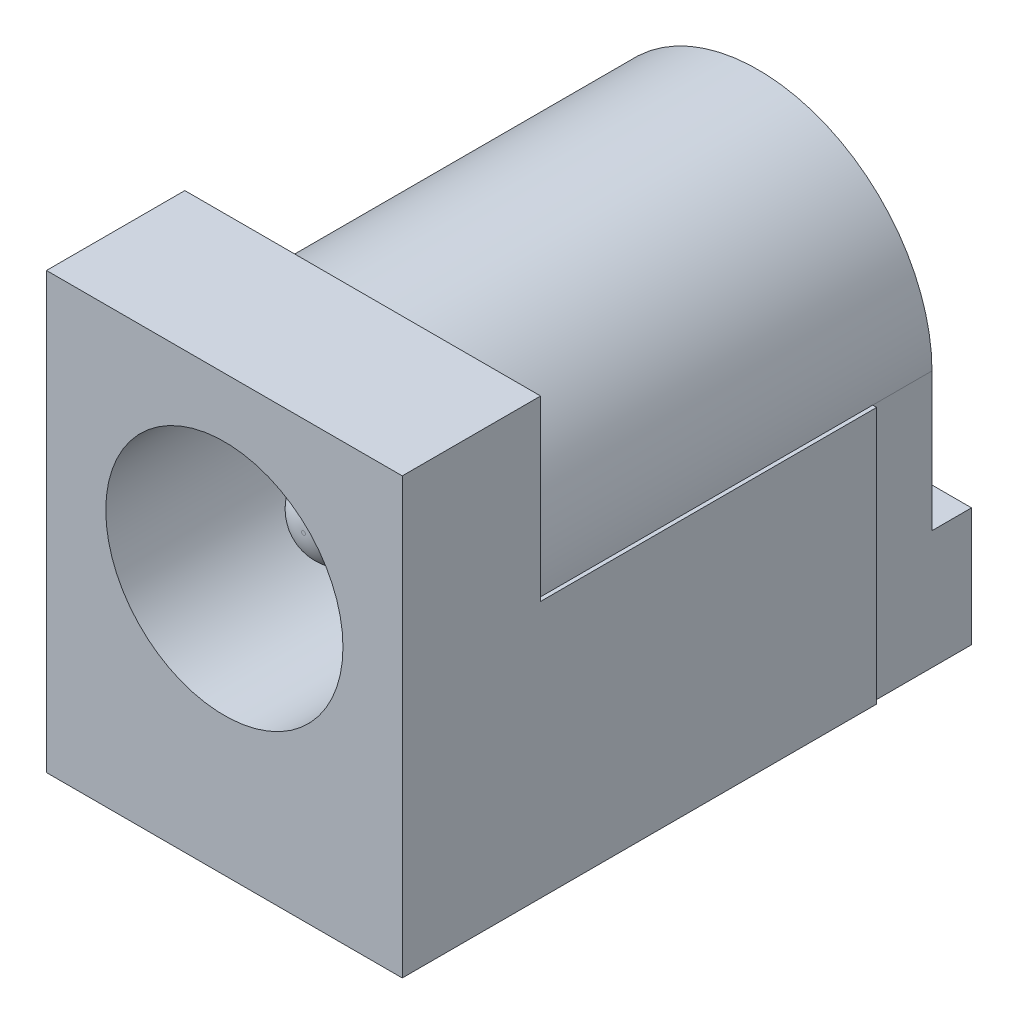
SolidWorks part; units mm, degrees
ref_plane "Front Plane" through (0, 0, 0) normal (0, 0, 1) x (1, 0, 0)
ref_plane "Top Plane" through (0, 0, 0) normal (0, 1, 0) x (1, 0, 0)
ref_plane "Right Plane" through (0, 0, 0) normal (1, 0, 0) x (0, 0, -1)
sketch "Sketch1" plane through (0, 0, 0) normal (1, 0, 0) x (0, 0, -1)
  line L1 (0, 0) -> (14.5, 0)
  line L2 (0, 0) -> (0, 11)
  line L3 (0, 11) -> (14.5, 11)
  line L4 (14.5, 0) -> (14.5, 11)
  dimension "D1" = 11
  dimension "D2" = 14.5
extrude "Boss-Extrude1" add sketch "Sketch1" along normal blind 9
sketch "Sketch2" plane through (0, 0, -14.5) normal (0, 0, -1) x (-1, 0, 0)
  line L0 (-8.9, 6.5) -> (-9, 6.5)
  line L4 (-9, 0) -> (-9, 11) construction
  line L5 (-0.1, 6.5) -> (0, 6.5)
  line L6 (0, 0) -> (0, 11) construction
  line L7 (-9, 11) -> (0, 11) construction
  arc A0 (-8.9, 6.5) -> (-0.1, 6.5) centre (-4.5, 6.5) cw
  dimension "D2" = 4.4
  dimension "D1" = 4.5
  dimension "D3" = 0.1
extrude "Cut-Extrude1" cut sketch "Sketch2" against normal blind 11 and the other way through all
sketch "Sketch5" plane through (0, 0, 0) normal (-1, 0, 0) x (0, 0, 1)
  line L0 (-14.5, 6.5) -> (-3.5, 6.5) construction
  line L1 (-14.5, 0) -> (-12, 0)
  line L2 (-14.5, 0) -> (-14.5, 6.5)
  line L3 (-14.5, 6.5) -> (-12, 6.5)
  line L4 (-12, 0) -> (-12, 6.5)
  dimension "D1" = 2.5
extrude "Cut-Extrude2" cut sketch "Sketch5" against normal blind 0.1
sketch "Sketch6" plane through (9, 0, 0) normal (1, 0, 0) x (0, 0, -1)
  line L0 (14.5, 6.5) -> (3.5, 6.5) construction
  line L1 (14.5, 0) -> (12, 0)
  line L2 (14.5, 0) -> (14.5, 6.5)
  line L3 (14.5, 6.5) -> (12, 6.5)
  line L4 (12, 0) -> (12, 6.5)
  dimension "D1" = 2.5
extrude "Cut-Extrude3" cut sketch "Sketch6" against normal blind 0.1
sketch "Sketch7" plane through (0, 0, -14.5) normal (0, 0, -1) x (-1, 0, 0)
  line L2 (-8.9, 6.5) -> (-8.9, 0)
  line L3 (-8.9, 0) -> (-0.1, 0)
  line L4 (-0.1, 6.5) -> (-0.1, 0)
  arc A0 (-8.9, 6.5) -> (-0.1, 6.5) centre (-4.5, 6.5) cw
  arc A1 (-0.1, 6.5) -> (-8.9, 6.5) centre (-4.5, 6.5) ccw construction
  dimension "D1" = 4.4
extrude "Cut-Extrude4" cut sketch "Sketch7" against normal blind 1
sketch "Sketch8" plane through (0, 0, -13.5) normal (0, 0, -1) x (-1, 0, 0)
  line L1 (-8.9, 0) -> (-6, 0)
  line L2 (-8.9, 0) -> (-8.9, 3)
  line L3 (-8.9, 3) -> (-6, 3)
  line L4 (-6, 0) -> (-6, 3)
  line L5 (-0.1, 0) -> (-3, 0)
  line L6 (-0.1, 0) -> (-0.1, 3)
  line L7 (-0.1, 3) -> (-3, 3)
  line L8 (-3, 0) -> (-3, 3)
  dimension "D1" = 3
  dimension "D2" = 2.9
  dimension "D3" = 2.9
  dimension "D4" = 3
extrude "Boss-Extrude2" add sketch "Sketch8" along normal blind 1
sketch "Sketch9" plane through (0, 0, 0) normal (0, 0, 1) x (1, 0, 0)
  line L0 (9, 11) -> (0, 11) construction
  line L1 (0, 11) -> (0, 0) construction
  circle A0 centre (4.5, 6.5) radius 3
  dimension "D3" = 6
  dimension "D1" = 4.5
  dimension "D2" = 4.5
extrude "Cut-Extrude5" cut sketch "Sketch9" against normal blind 12
sketch "Sketch10" plane through (0, 0, -13.5) normal (0, 0, -1) x (-1, 0, 0)
  line L2 (-9, 11) -> (0, 11) construction
  line L4 (-6, 0) -> (-6, 5.3176)
  line L6 (-2.9977, 0) -> (-2.9977, 5.3204)
  line L8 (-9, 6.5) -> (-9, 0) construction
  line L11 (-6, 0) -> (-6, -3.5)
  line L12 (-6, -3.5) -> (-2.9977, -3.5)
  line L13 (-2.9977, 0) -> (-2.9977, -3.5)
  arc A1 (-6, 5.3176) -> (-2.9977, 5.3204) centre (-4.5, 6.5) cw
  dimension "D4" = 5.3204
  dimension "D3" = 1.91
  dimension "D1" = 4.5
  dimension "D2" = 4.5
  dimension "D5" = 3.5
  dimension "D6" = 3.5
extrude "Boss-Extrude4" add sketch "Sketch10" along normal blind 0.4 separate body
sketch "Sketch11" plane through (0, 0, -13.9) normal (0, 0, -1) x (-1, 0, 0)
  line L0 (-3, 0) -> (-0.1, 0) construction
  line L2 (-9, 6.5) -> (-9, 0) construction
  circle A0 centre (-4.5, 1.5) radius 0.5
  dimension "D3" = 1
  dimension "D1" = 1.5
  dimension "D2" = 4.5
extrude "Boss-Extrude5" add sketch "Sketch11" along normal blind 0.1 draft 80
fillet "Fillet1" radius 1.4 2 edges at (6, -3.5, -13.7) (2.9977, -3.5, -13.7)
sketch "Sketch12" plane through (0, 0, -13.9) normal (0, 0, -1) x (-1, 0, 0)
  line L0 (-4.6, -3.5) -> (-4.3977, -3.5) construction
  circle A0 centre (-4.4747, -2) radius 0.8
  dimension "D2" = 1.6
  dimension "D1" = 1.5
extrude "Cut-Extrude6" cut sketch "Sketch12" against normal blind 0.4
sketch "Sketch13" plane through (0, 0, -13.9) normal (0, 0, -1) x (-1, 0, 0)
  line L0 (-9, 6.5) -> (-9, 11) construction
  line L1 (-9, 11) -> (0, 11) construction
  circle A0 centre (-4.5042, 6.5) radius 1.5
  circle A1 centre (-4.5042, 6.5) radius 1
  dimension "D3" = 3
  dimension "D4" = 2
  dimension "D1" = 4.4958
  dimension "D2" = 4.5
extrude "Boss-Extrude6" add sketch "Sketch13" along normal blind 0.2 draft 35 separate body
sketch "Sketch14" plane through (0, 0, -13.9) normal (0, 0, -1) x (-1, 0, 0)
  circle A0 centre (-4.5042, 6.5) radius 0.8
  dimension "D1" = 1.6
extrude "Cut-Extrude7" cut sketch "Sketch14" against normal blind 0.1 draft 85
sketch "Sketch16" plane through (0, 0, 0) normal (0, -1, 0) x (1, 0, 0)
  line L0 (9, 0) -> (0, 0) construction
  line L1 (3.25, -7.7) -> (5.75, -7.7)
  line L2 (3.25, -7.7) -> (3.25, -8.1)
  line L3 (3.25, -8.1) -> (5.75, -8.1)
  line L4 (5.75, -7.7) -> (5.75, -8.1)
  line L5 (0, 0) -> (0, -12) construction
  dimension "D1" = 7.7
  dimension "D2" = 2.5
  dimension "D3" = 3.25
  dimension "D4" = 0.4
extrude "Boss-Extrude7" add sketch "Sketch16" along normal blind 3.5
sketch "Sketch18" plane through (0, 0, -7.7) normal (0, 0, 1) x (1, 0, 0)
  line L0 (5.75, -3.5) -> (3.25, -3.5) construction
  line L1 (5.75, -3.5) -> (5.75, 0) construction
  circle A0 centre (4.5, -2) radius 0.8
  dimension "D2" = 1.6
  dimension "D1" = 1.5
  dimension "D3" = 1.25
extrude "Cut-Extrude8" cut sketch "Sketch18" against normal blind 0.4
fillet "Fillet2" radius 1.1 2 edges at (3.25, -3.5, -7.9) (5.75, -3.5, -7.9)
sketch "Sketch19" plane through (0, 0, -12) normal (0, 0, 1) x (1, 0, 0)
  line L0 (9, 11) -> (9, 0) construction
  line L1 (9, 11) -> (0, 11) construction
  circle A0 centre (4.5, 6.5) radius 1.05
  dimension "D3" = 2.1
  dimension "D1" = 4.5
  dimension "D2" = 4.5
extrude "Boss-Extrude8" add sketch "Sketch19" along normal blind 10
fillet "Fillet3" radius 1 1 edges at (5.55, 6.5, -2)
